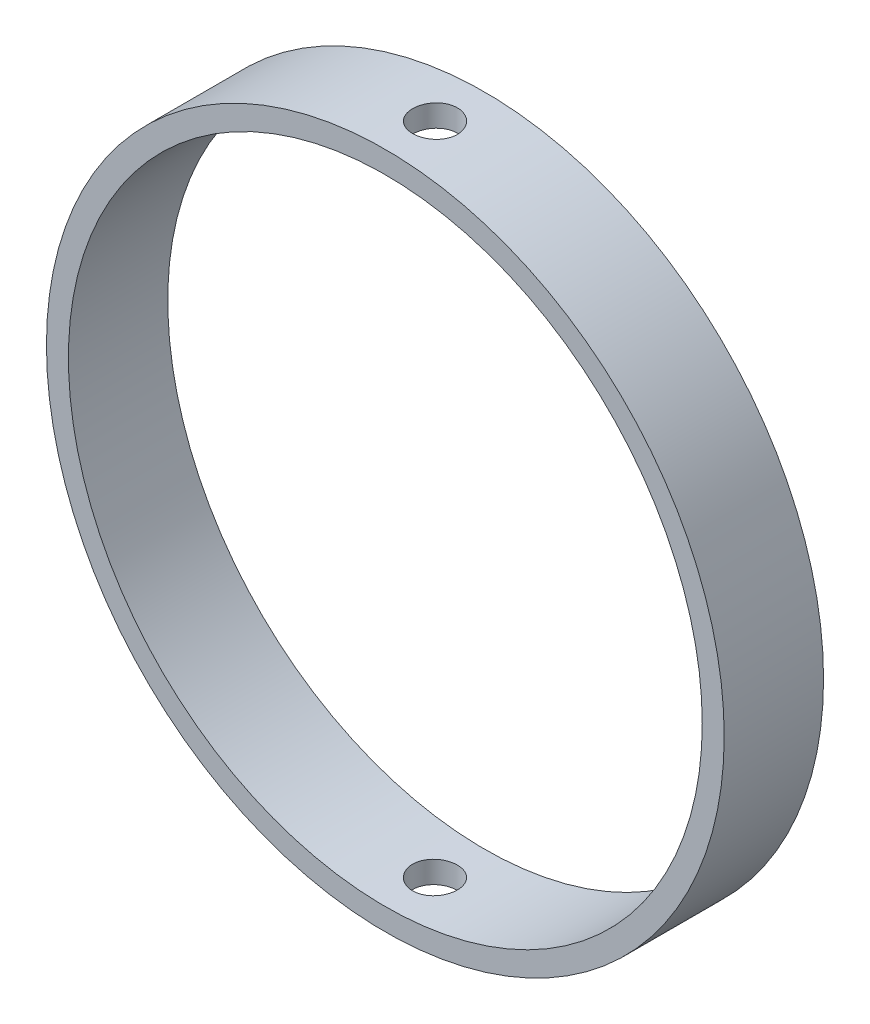
SolidWorks part; units mm, degrees
ref_plane "Front Plane" through (0, 0, 0) normal (0, 0, 1) x (1, 0, 0)
ref_plane "Top Plane" through (0, 0, 0) normal (0, 1, 0) x (1, 0, 0)
ref_plane "Right Plane" through (0, 0, 0) normal (1, 0, 0) x (0, 0, -1)
sketch "Sketch1" plane through (0, 0, 0) normal (0, 0, 1) x (1, 0, 0)
  circle A0 centre (0, 0) radius 34.11
  circle A1 centre (0, 0) radius 31.9
  dimension "D1" = 68.22
  dimension "D2" = 63.8
extrude "Boss-Extrude1" add sketch "Sketch1" along normal blind 10
ref_plane "Plane1" through (0, 34.11, 0) normal (0, 1, 0) x (1, 0, 0)
sketch "Sketch2" plane through (0, 34.11, 0) normal (0, 1, 0) x (1, 0, 0)
  circle A0 centre (0, -5) radius 2.25
  dimension "D1" = 4.5
  dimension "D2" = 5
extrude "Cut-Extrude1" cut sketch "Sketch2" against normal through all
